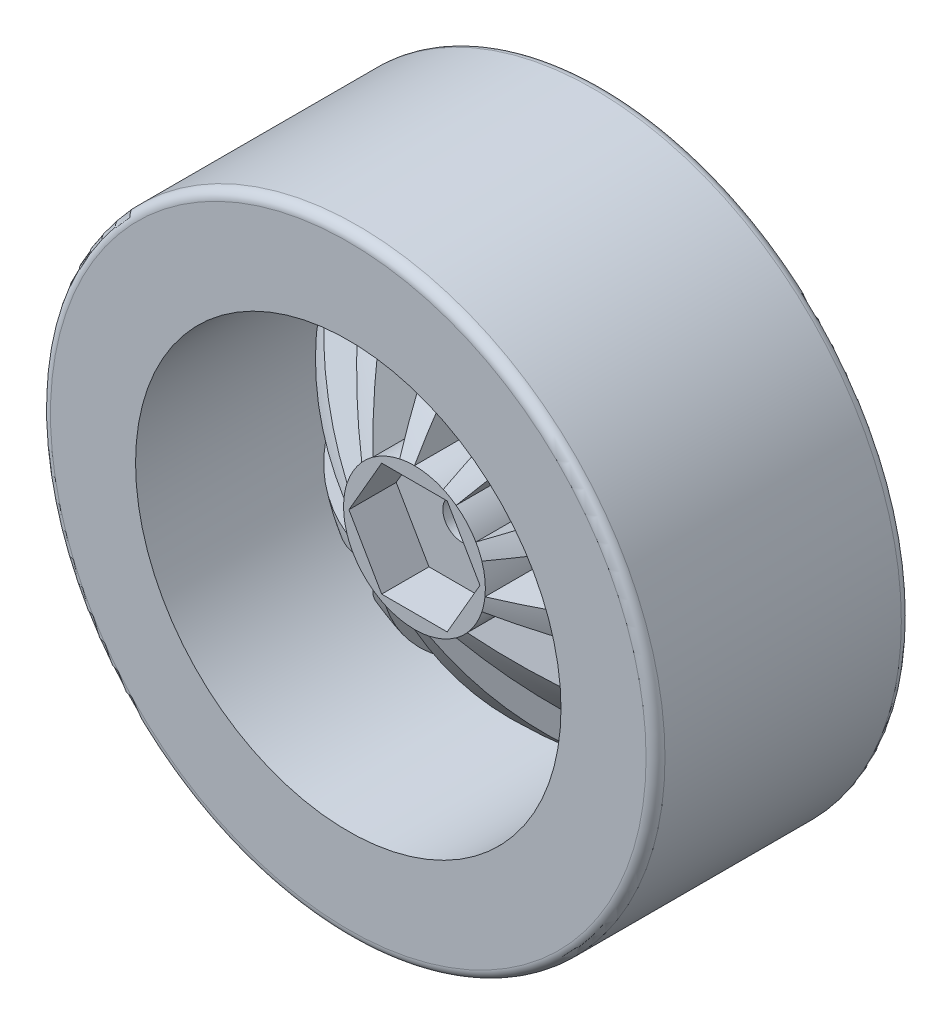
SolidWorks part; units mm, degrees
ref_plane "前视基准面" through (0, 0, 0) normal (0, 0, 1) x (1, 0, 0)
ref_plane "上视基准面" through (0, 0, 0) normal (0, 1, 0) x (1, 0, 0)
ref_plane "右视基准面" through (0, 0, 0) normal (1, 0, 0) x (0, 0, -1)
ref_axis "基准轴1" through (0, 0, -16.35) along (0, 0, 1)
sketch "草图1" plane through (0, 0, 0) normal (0, 0, 1) x (1, 0, 0)
  line L1 (-6.9282, 0) -> (-3.4641, -6)
  line L2 (-3.4641, -6) -> (3.4641, -6)
  line L3 (3.4641, -6) -> (6.9282, 0)
  line L4 (6.9282, 0) -> (3.4641, 6)
  line L5 (3.4641, 6) -> (-3.4641, 6)
  line L6 (-3.4641, 6) -> (-6.9282, 0)
  circle A2 centre (0, 0) radius 7.5
  circle A3 centre (0, 0) radius 6 construction
  dimension "D1" = 15
  dimension "D2" = 12
extrude "凸台-拉伸1" add sketch "草图1" along normal blind 5
sketch "草图2" plane through (0, 0, 0) normal (0, 0, 1) x (1, 0, 0)
  circle A0 centre (0, 0) radius 7.5
  circle A1 centre (0, 0) radius 2
extrude "凸台-拉伸2" add sketch "草图2" against normal blind 3
sketch "草图3" plane through (0, 0, 0) normal (0, 0, 1) x (1, 0, 0)
  circle A0 centre (0, 0) radius 32.5
  circle A1 centre (0, 0) radius 22.5
  dimension "D1" = 65
  dimension "D2" = 45
extrude "凸台-拉伸3" add sketch "草图3" along normal blind 12 and the other way blind 15 separate body
sketch "草图4" plane through (0, 0, 0) normal (1, 0, 0) x (0, 0, -1)
  line L4 (-5, 7.5) -> (3, 7.5)
  line L6 (15, 22.5) -> (3, 7.5) construction
  line L7 (-5, 7.5) -> (7, 22.5) construction
  line L8 (15, 22.5) -> (7, 22.5)
  arc A0 (15, 22.5) -> (3, 7.5) centre (25.9531, 1.4376) ccw
  arc A1 (7, 22.5) -> (-5, 7.5) centre (49.2538, -23.603) ccw
  dimension "D2" = 7.5
  dimension "D3" = 8
  dimension "D5" = 3
revolve "旋转1" add sketch "草图4" angle 12 about axis through (0, 0, -16.35) along (0, 0, 1)
pattern_circular "阵列(圆周)1" count 10 over 360 about axis through (0, 0, 0) along (0, 0, 1) of "旋转1"
sketch "草图5" plane through (0, 0, -3) normal (0, 0, -1) x (-1, 0, 0)
  circle A0 centre (0, 0) radius 4.5
  dimension "D1" = 9
extrude "切除-拉伸1" cut sketch "草图5" against normal blind 2
fillet "圆角1" radius 1 2 edges at (32.5, 0, 12) (32.5, 0, -15)
